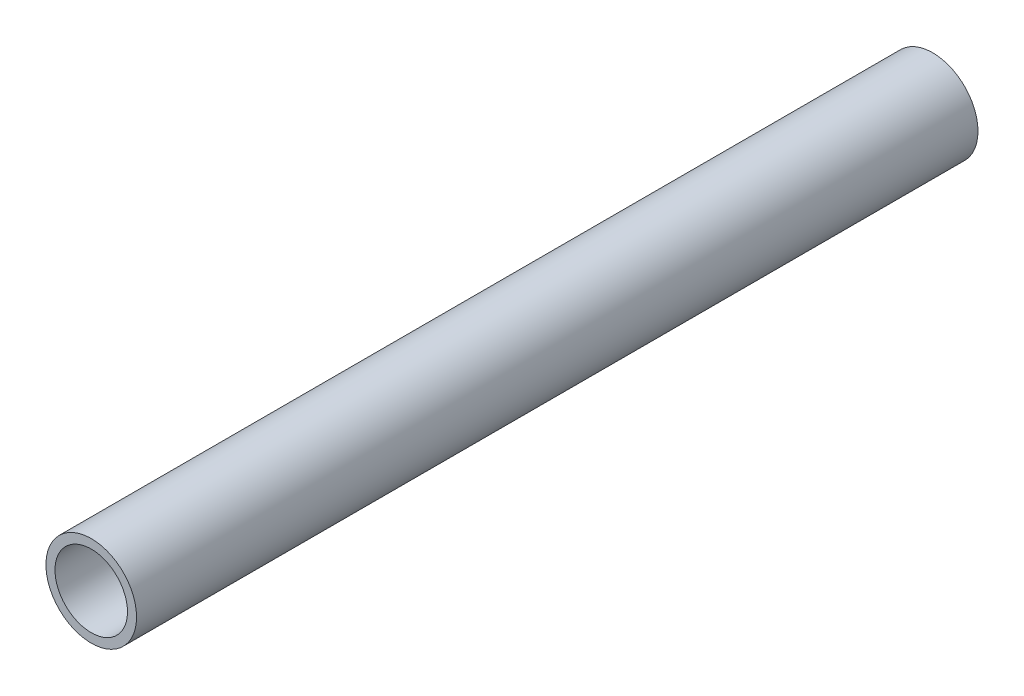
SolidWorks part; units mm, degrees
ref_plane "Front Plane" through (0, 0, 0) normal (0, 0, 1) x (1, 0, 0)
ref_plane "Top Plane" through (0, 0, 0) normal (0, 1, 0) x (1, 0, 0)
ref_plane "Right Plane" through (0, 0, 0) normal (1, 0, 0) x (0, 0, -1)
sketch "Sketch1" plane through (0, 0, 0) normal (0, 0, 1) x (1, 0, 0)
  circle A0 centre (0, 0) radius 1.25
  circle A1 centre (0, 0) radius 1
extrude "Boss-Extrude1" add sketch "Sketch1" along normal blind 23.21
equation "\"D1@Boss-Extrude1\"= \"HL@parametersSketch@prostheticParameters.SLDPRT\" * 0.266 - 12 - 4 - 10"
